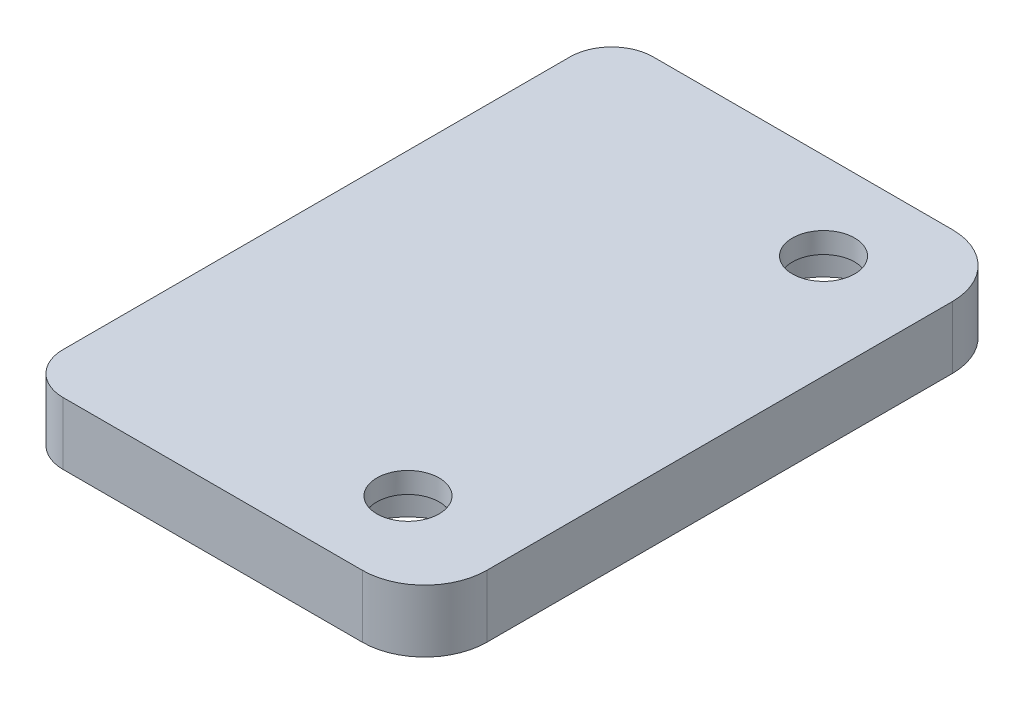
SolidWorks part; units mm, degrees
ref_plane "Front Plane" through (0, 0, 0) normal (0, 0, 1) x (1, 0, 0)
ref_plane "Top Plane" through (0, 0, 0) normal (0, 1, 0) x (1, 0, 0)
ref_plane "Right Plane" through (0, 0, 0) normal (1, 0, 0) x (0, 0, -1)
sketch "Sketch1" plane through (0, 0, 0) normal (0, 1, 0) x (1, 0, 0)
  line L1 (9.7, 14.2) -> (-9.7, 14.2)
  line L2 (9.7, 14.2) -> (9.7, -14.2)
  line L3 (9.7, -14.2) -> (-9.7, -14.2)
  line L4 (-9.7, 14.2) -> (-9.7, -14.2)
  line L5 (9.7, 14.2) -> (-9.7, -14.2) construction
  line L6 (9.7, -14.2) -> (-9.7, 14.2) construction
  point P0 (0, 0)
  dimension "D1" = 28.4
  dimension "D2" = 19.4
extrude "Boss-Extrude1" add sketch "Sketch1" along normal blind 3
fillet "Fillet1" radius 3 2 edges at (9.7, 1.5, -14.2) (9.7, 1.5, 14.2)
fillet "Fillet2" radius 2 2 edges at (-9.7, 1.5, -14.2) (-9.7, 1.5, 14.2)
sketch "Sketch2" plane through (0, 3, 0) normal (0, 1, 0) x (1, 0, 0)
  line L0 (0, 0) -> (11.3649, 0) construction
  line L1 (9.7, -11.2) -> (9.7, 11.2) construction
  circle A0 centre (4.7, 10) radius 1.5
  circle A1 centre (4.7, -10) radius 1.5
  dimension "D2" = 3
  dimension "D3" = 5
  dimension "D1" = 20
extrude "Cut-Extrude1" cut sketch "Sketch2" against normal through all
sketch "Sketch4" plane through (0, 0, 0) normal (0, -1, 0) x (1, 0, 0)
  circle A0 centre (4.7, 10) radius 3
  circle A1 centre (4.7, -10) radius 3
  dimension "D1" = 6
extrude "Cut-Extrude2" cut sketch "Sketch4" against normal blind 2
